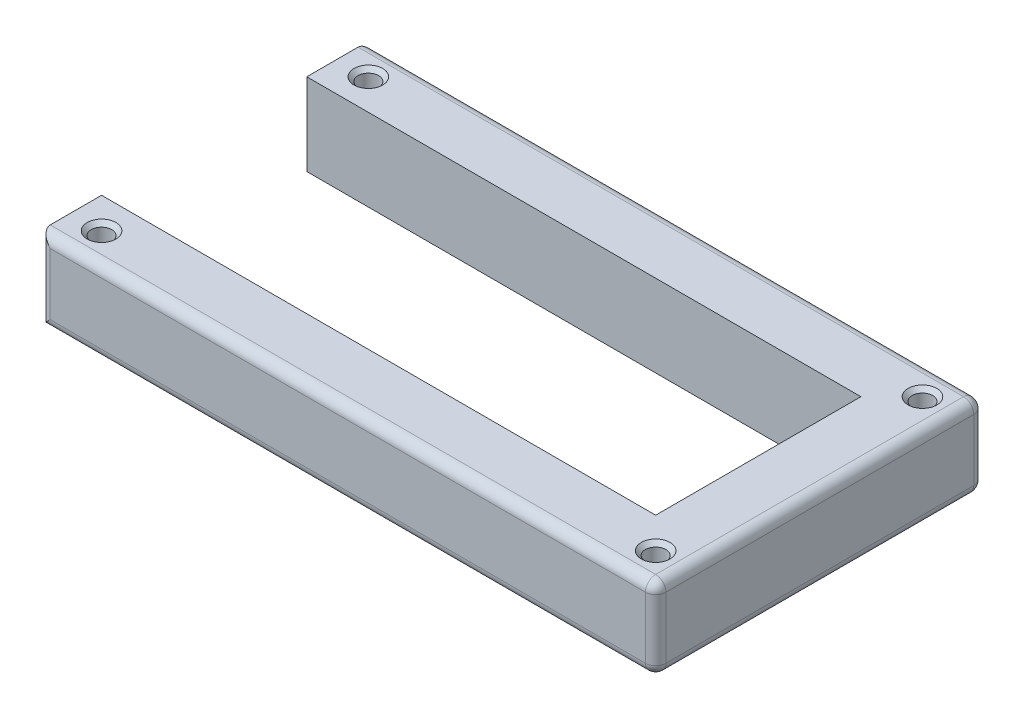
SolidWorks part; units mm, degrees
ref_plane "Front Plane" through (0, 0, 0) normal (0, 0, 1) x (1, 0, 0)
ref_plane "Top Plane" through (0, 0, 0) normal (0, 1, 0) x (1, 0, 0)
ref_plane "Right Plane" through (0, 0, 0) normal (1, 0, 0) x (0, 0, -1)
sketch "Sketch1" plane through (0, 0, 0) normal (0, 1, 0) x (1, 0, 0)
  line L0 (-150, 0) -> (0, 0) construction
  line L1 (0, 25) -> (-135, 25)
  line L3 (15, 40) -> (-135, 40)
  line L4 (-135, 25) -> (-135, 40)
  line L9 (-135, -25) -> (-135, -40)
  line L10 (15, -40) -> (-135, -40)
  line L12 (0, -25) -> (-135, -25)
  line L15 (15, -40) -> (15, 40)
  line L17 (0, -25) -> (0, 25)
  point P0 (-150, 0)
  dimension "D1" = 15
  dimension "D2" = 135
  dimension "D3" = 150
  dimension "D4" = 50
  dimension "D5" = 80
extrude "Boss-Extrude1" add sketch "Sketch1" along normal blind 20
fillet "Fillet1" radius 2.5 10 edges at (-60, 20, -40) (-135, 10, -40) (-60, 0, -40) (15, 20, 0) (15, 10, -40) (15, 0, 0) (-135, 10, 40) (-60, 20, 40) (15, 10, 40) (-60, 0, 40)
sketch "Sketch2" plane through (0, 20, 0) normal (0, 1, 0) x (1, 0, 0)
  line L0 (-132.5, 40) -> (12.5, 40) construction
  line L1 (15, 37.5) -> (15, -37.5) construction
  line L6 (-153.3982, 0) -> (0, 0) construction
  line L7 (-135, -25) -> (-135, -37.5) construction
  line L8 (-135, 37.5) -> (-135, 25) construction
  line L9 (12.5, -40) -> (-132.5, -40) construction
  circle A0 centre (7.5, 32.5) radius 2.5
  circle A2 centre (7.5, -32.5) radius 2.5
  circle A3 centre (-127.5, 32.5) radius 2.5
  circle A4 centre (-127.5, -32.5) radius 2.5
  point P21 (0, 0)
  dimension "D1" = 7.5
  dimension "D3" = 5
  dimension "D8" = 5
  dimension "D2" = 7.5
  dimension "D4" = 7.5
  dimension "D5" = 7.5
  dimension "D6" = 7.5
  dimension "D7" = 7.5
extrude "Cut-Extrude1" cut sketch "Sketch2" against normal through all
chamfer "Chamfer1" distance 1 angle 45 4 edges at (7.5, 20, -30) (7.5, 20, 30) (-127.5, 20, 35) (-127.5, 20, -30)
